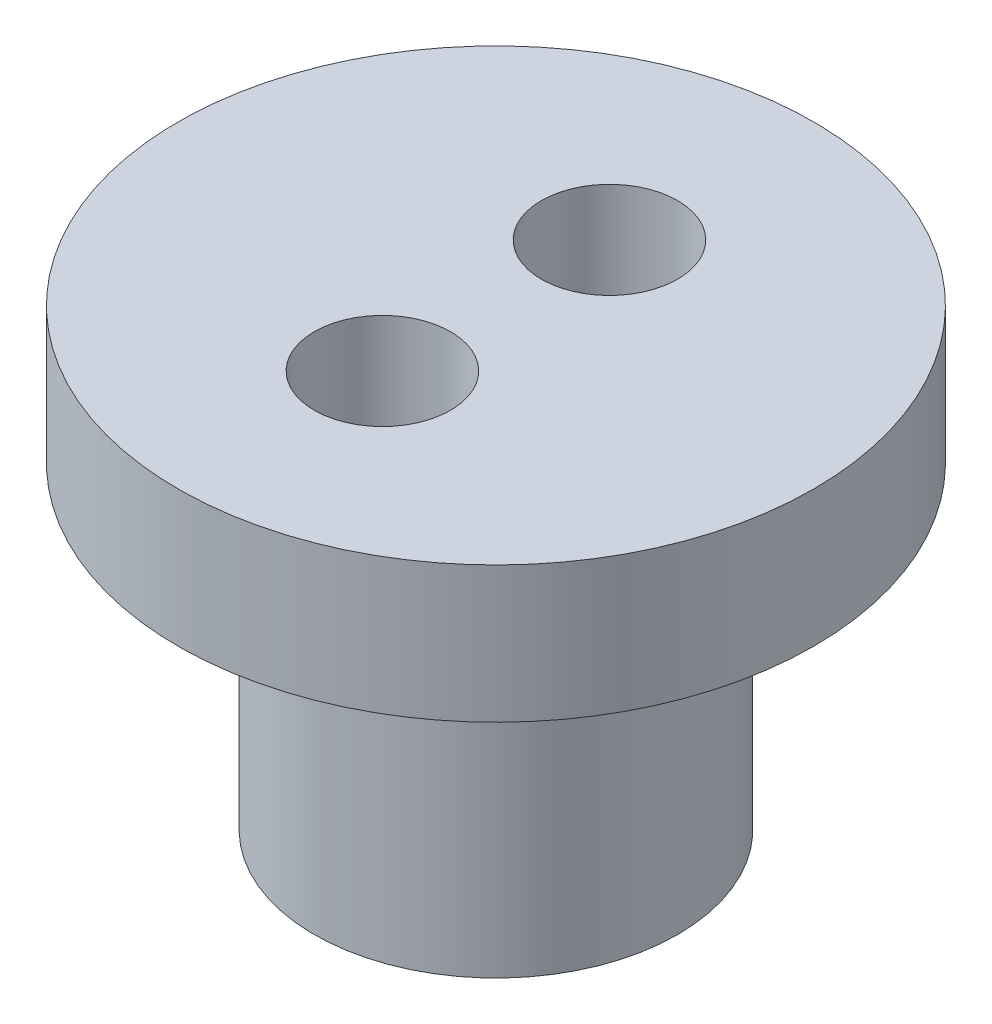
SolidWorks part; units mm, degrees
ref_plane "Front Plane" through (0, 0, 0) normal (0, 0, 1) x (1, 0, 0)
ref_plane "Top Plane" through (0, 0, 0) normal (0, 1, 0) x (1, 0, 0)
ref_plane "Right Plane" through (0, 0, 0) normal (1, 0, 0) x (0, 0, -1)
sketch "Sketch1" plane through (0, 0, 0) normal (0, 0, 1) x (1, 0, 0)
  line L0 (2, 0) -> (2, 4)
  line L1 (2, 4) -> (0, 4)
  line L2 (0, 4) -> (0, 10)
  line L3 (0, 10) -> (7, 10)
  line L4 (7, 10) -> (7, 7)
  line L5 (7, 7) -> (4, 7)
  line L6 (4, 7) -> (4, 0)
  line L7 (4, 0) -> (2, 0)
  dimension "D1" = 2
  dimension "D2" = 7
  dimension "D3" = 7
  dimension "D4" = 4
  dimension "D5" = 3
  dimension "D6" = 4
revolve "Revolve1" add sketch "Sketch1" angle 360 about L2
fillet "Fillet1" radius 1 1 edges at (4, 7, 0)
sketch "Sketch2" plane through (0, 10, 0) normal (0, 1, 0) x (1, 0, 0)
  circle A0 centre (0, 2.5) radius 1.5
  circle A1 centre (0, -2.5) radius 1.5
  dimension "D1" = 3
  dimension "D2" = 5
  dimension "D3" = 2.5
extrude "Cut-Extrude1" cut sketch "Sketch2" against normal blind 3
equation "\"D3@Sketch2\"=\"D2@Sketch2\"/2"
